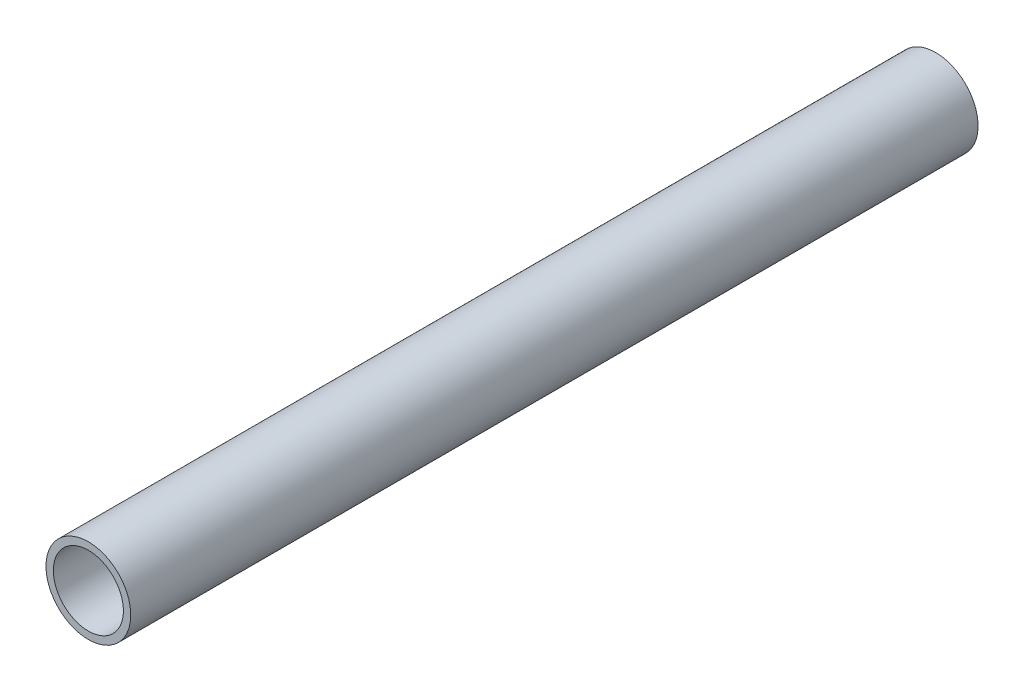
SolidWorks part; units mm, degrees
material "Plain Carbon Steel"
ref_plane "Front Plane" through (0, 0, 0) normal (0, 0, 1) x (1, 0, 0)
ref_plane "Top Plane" through (0, 0, 0) normal (0, 1, 0) x (1, 0, 0)
ref_plane "Right Plane" through (0, 0, 0) normal (1, 0, 0) x (0, 0, -1)
sketch "Sketch1" plane through (0, 0, 0) normal (1, 0, 0) x (0, 0, -1)
  line L0 (0, 0) -> (-50000, 0) construction
  line L1 (-95.25, 7.874) -> (95.25, 7.874)
  line L2 (95.25, 9.525) -> (-95.25, 9.525)
  line L3 (-95.25, 9.525) -> (-95.25, 7.874)
  line L4 (95.25, 7.874) -> (95.25, 9.525)
  point P5 (0, 7.874)
  dimension "D1" = 9.525
  dimension "D2" = 1.651
  dimension "D3" = 190.5
revolve "Revolve1" add sketch "Sketch1" angle 360 about L0
